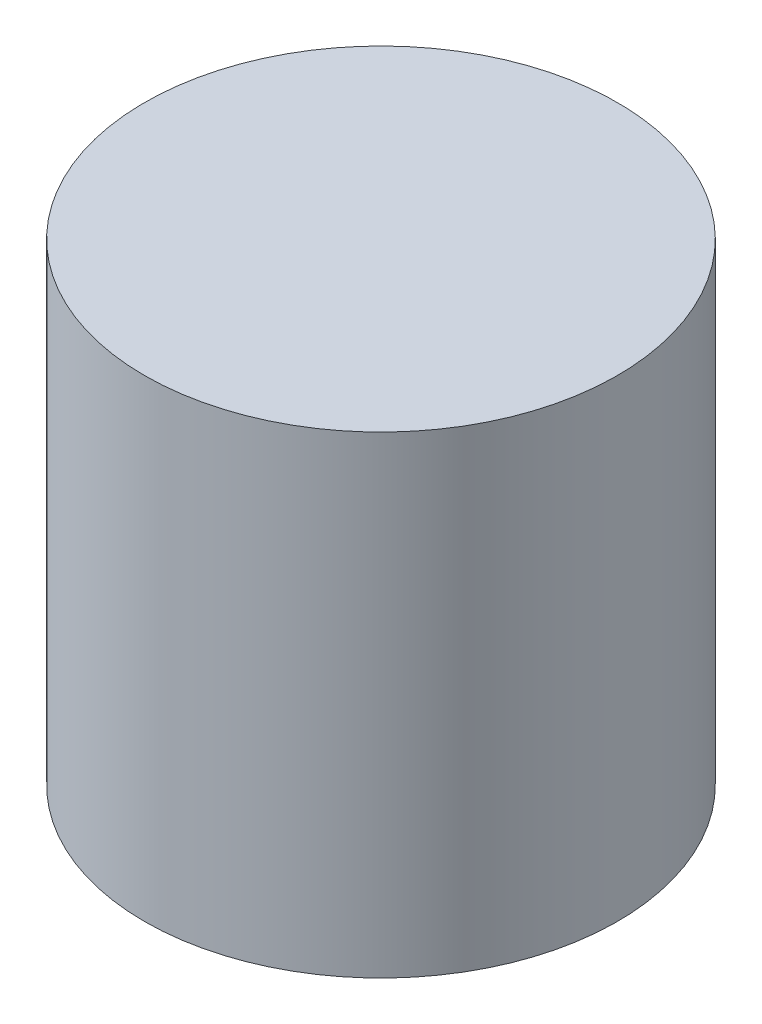
SolidWorks part; units mm, degrees
ref_plane "Спереди" through (0, 0, 0) normal (0, 0, 1) x (1, 0, 0)
ref_plane "Сверху" through (0, 0, 0) normal (0, 1, 0) x (1, 0, 0)
ref_plane "Справа" through (0, 0, 0) normal (1, 0, 0) x (0, 0, -1)
sketch "Sketch1" plane through (0, 0, 0) normal (0, 1, 0) x (1, 0, 0)
  circle A0 centre (0, 0) radius 10
  dimension "D1" = 20
extrude "Boss-Extrude1" add sketch "Sketch1" along normal blind 20
sketch "Sketch2" plane through (0, 0, 0) normal (0, -1, 0) x (1, 0, 0)
  circle A0 centre (0, 0) radius 3.125
  dimension "D1" = 6.25
extrude "Cut-Extrude1" cut sketch "Sketch2" against normal blind 17
sketch "Sketch3" plane through (0, 0, 0) normal (0, -1, 0) x (1, 0, 0)
  circle A0 centre (0, 0) radius 6
  dimension "D1" = 12
extrude "Cut-Extrude2" cut sketch "Sketch3" against normal blind 4
